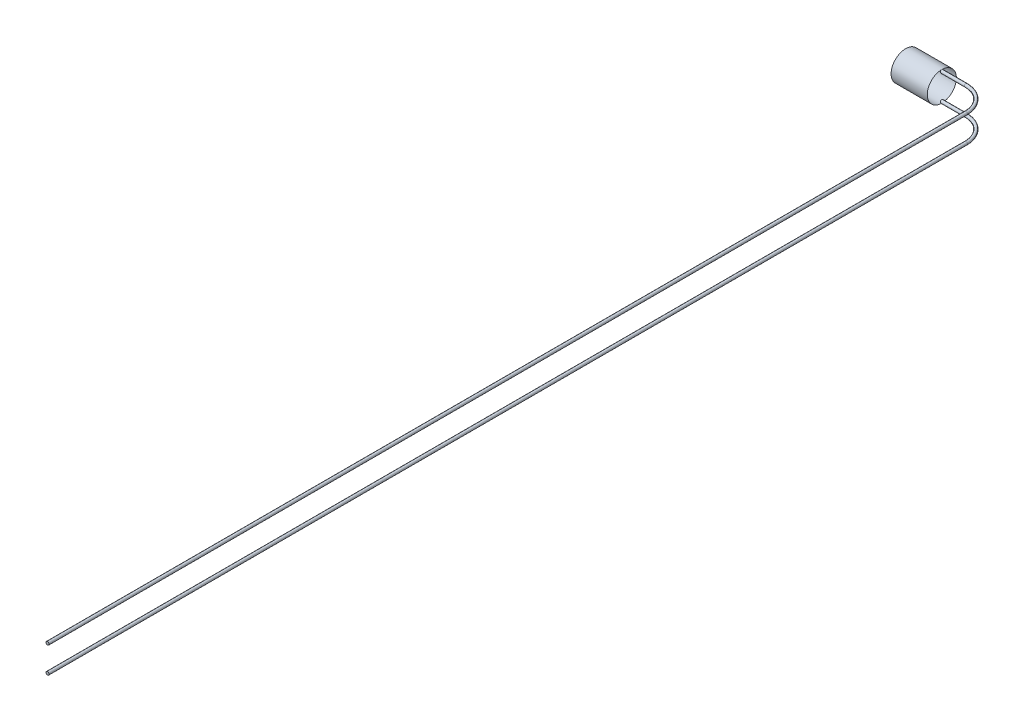
SolidWorks part; units mm, degrees
ref_plane "Front Plane" through (0, 0, 0) normal (0, 0, 1) x (1, 0, 0)
ref_plane "Top Plane" through (0, 0, 0) normal (0, 1, 0) x (1, 0, 0)
ref_plane "Right Plane" through (0, 0, 0) normal (1, 0, 0) x (0, 0, -1)
sketch "Sketch1" plane through (0, 0, 0) normal (0, 0, 1) x (1, 0, 0)
  line L0 (0, 0) -> (31.3061, 0) construction
  line L1 (-3, 1.2065) -> (0, 1.2065)
  line L2 (-3, 1.2065) -> (-3, 0)
  line L3 (-3, 0) -> (0, 0)
  line L4 (0, 1.2065) -> (0, 0)
  dimension "D1" = 2.413
  dimension "D2" = 3
revolve "Revolve1" add sketch "Sketch1" angle 360 about L0
sketch "Sketch2" plane through (0, 0, 0) normal (1, 0, 0) x (0, 0, -1)
  line L0 (0, -1.0795) -> (0, 1.0795) construction
  line L1 (0, 0) -> (3.2261, 0) construction
  circle A0 centre (0, 1.0795) radius 0.127
  circle A1 centre (0, -1.0795) radius 0.127
  circle A2 centre (0, 0) radius 1.2065 construction
  dimension "D1" = 0.254
sketch "Sketch3" plane through (0, 0, 0) normal (0, 1, 0) x (1, 0, 0)
  line L0 (0, 0) -> (2, 0)
  line L1 (4, -2) -> (4, -78.2)
  arc A0 (2, 0) -> (4, -2) centre (2, -2) cw
  dimension "D3" = 2
  dimension "D1" = 76.2
  dimension "D2" = 2
sweep "Sweep1" add profiles "Sketch2" path "Sketch3"
